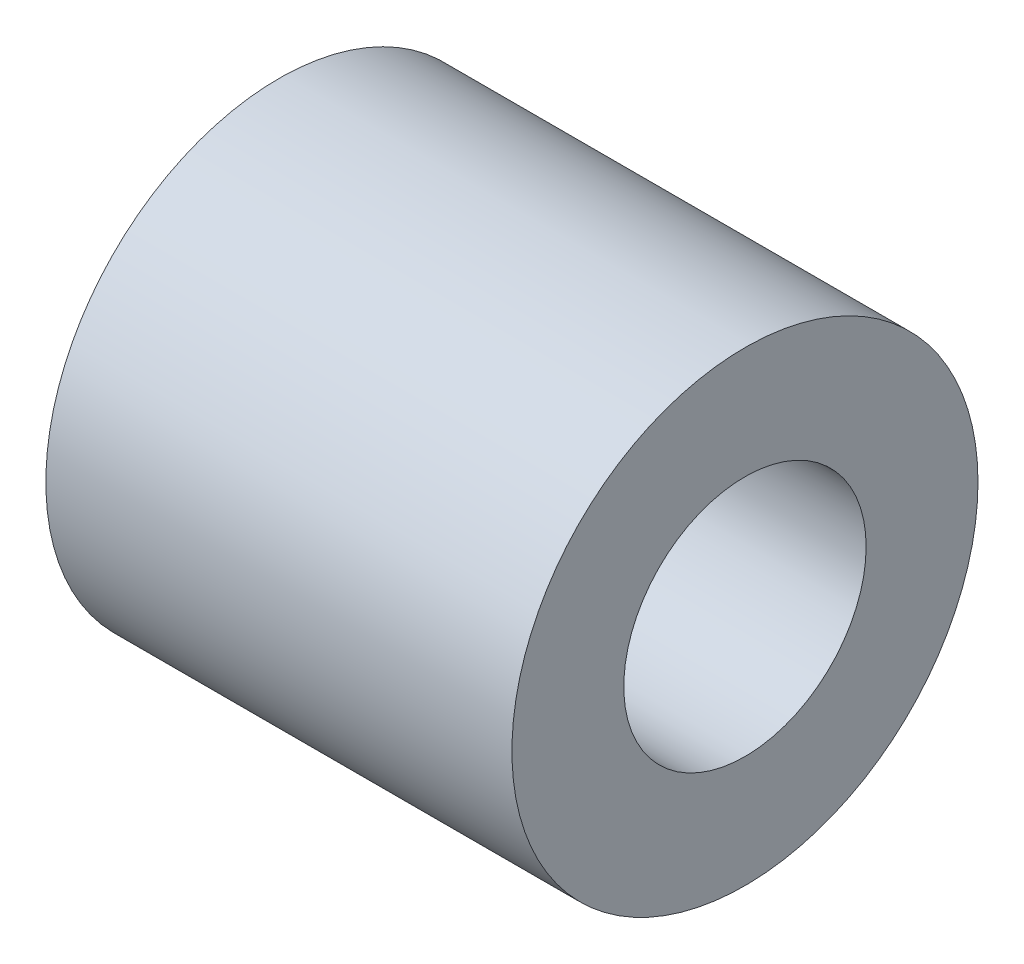
SolidWorks part; units mm, degrees
material "6061-T6 (SS)"
ref_plane "Front Plane" through (0, 0, 0) normal (0, 0, 1) x (1, 0, 0)
ref_plane "Top Plane" through (0, 0, 0) normal (0, 1, 0) x (1, 0, 0)
ref_plane "Right Plane" through (0, 0, 0) normal (1, 0, 0) x (0, 0, -1)
sketch "Sketch1" plane through (0, 0, 0) normal (1, 0, 0) x (0, 0, -1)
  circle A0 centre (0, 0) radius 3.175
  dimension "D1" = 6.35
extrude "Boss-Extrude1" add sketch "Sketch1" along normal blind 6.35
sketch "Sketch2" plane through (6.35, 0, 0) normal (1, 0, 0) x (0, 0, -1)
  circle A0 centre (0, 0) radius 1.651
  dimension "D1" = 3.302
extrude "Cut-Extrude1" cut sketch "Sketch2" against normal through all
